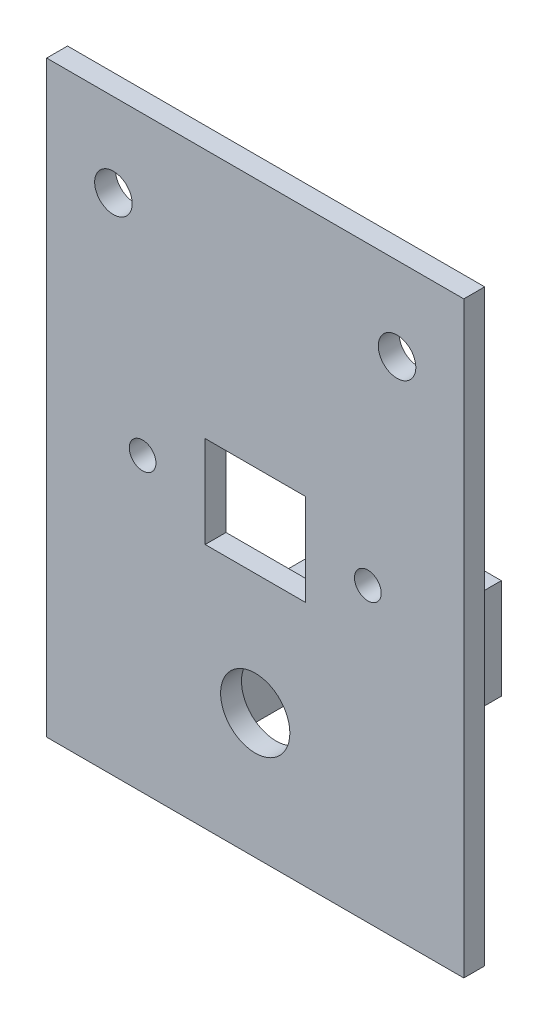
SolidWorks part; units mm, degrees
ref_plane "Front Plane" through (0, 0, 0) normal (0, 0, 1) x (1, 0, 0)
ref_plane "Top Plane" through (0, 0, 0) normal (0, 1, 0) x (1, 0, 0)
ref_plane "Right Plane" through (0, 0, 0) normal (1, 0, 0) x (0, 0, -1)
sketch "Sketch1" plane through (0, 0, 0) normal (0, 0, 1) x (1, 0, 0)
  line L1 (-25, -35.25) -> (25, -35.25)
  line L2 (-25, -35.25) -> (-25, 35.25)
  line L3 (-25, 35.25) -> (25, 35.25)
  line L4 (25, -35.25) -> (25, 35.25)
  line L5 (-25, -35.25) -> (25, 35.25) construction
  line L6 (-25, 35.25) -> (25, -35.25) construction
  line L7 (-6, -5.75) -> (6, -5.75)
  line L8 (-6, -5.75) -> (-6, 5.25)
  line L9 (-6, 5.25) -> (6, 5.25)
  line L10 (6, -5.75) -> (6, 5.25)
  line L11 (-6, -5.75) -> (6, 5.25) construction
  line L12 (-6, 5.25) -> (6, -5.75) construction
  circle A0 centre (-17, 25.25) radius 2.25
  circle A1 centre (17, 25.25) radius 2.25
  circle A2 centre (-13.5, -0.25) radius 1.6
  circle A3 centre (13.5, -0.25) radius 1.6
  circle A4 centre (0, -20.25) radius 4.15
  point P0 (0, 0)
  point P11 (0, -0.25)
  point P16 (0, 35.25)
  dimension "D5" = 4.5
  dimension "D11" = 3.2
  dimension "D12" = 8.3
  dimension "D1" = 50
  dimension "D2" = 10
  dimension "D3" = 8
  dimension "D4" = 8
  dimension "D6" = 30
  dimension "D7" = 12
  dimension "D8" = 11
  dimension "D9" = 13.5
  dimension "D10" = 13.5
  dimension "D13" = 20
  dimension "D14" = 15
extrude "Boss-Extrude1" add sketch "Sketch1" along normal blind 2.5
sketch "Sketch2" plane through (0, 0, 0) normal (0, 0, -1) x (-1, 0, 0)
  line L0 (5, -14.25) -> (7, -14.25)
  line L4 (5, -26.25) -> (5, -14.25)
  line L5 (7, -14.25) -> (7, -26.25)
  line L6 (7, -26.25) -> (5, -26.25)
  line L7 (0, -16.1) -> (0, -24.4) construction
  line L8 (-7, -14.25) -> (-7, -26.25)
  line L9 (-5, -14.25) -> (-7, -14.25)
  line L10 (-5, -26.25) -> (-5, -14.25)
  line L11 (-7, -26.25) -> (-5, -26.25)
  circle A0 centre (0, -20.25) radius 4.15 construction
  dimension "D2" = 12
  dimension "D3" = 2
extrude "Boss-Extrude2" add sketch "Sketch2" along normal blind 20
